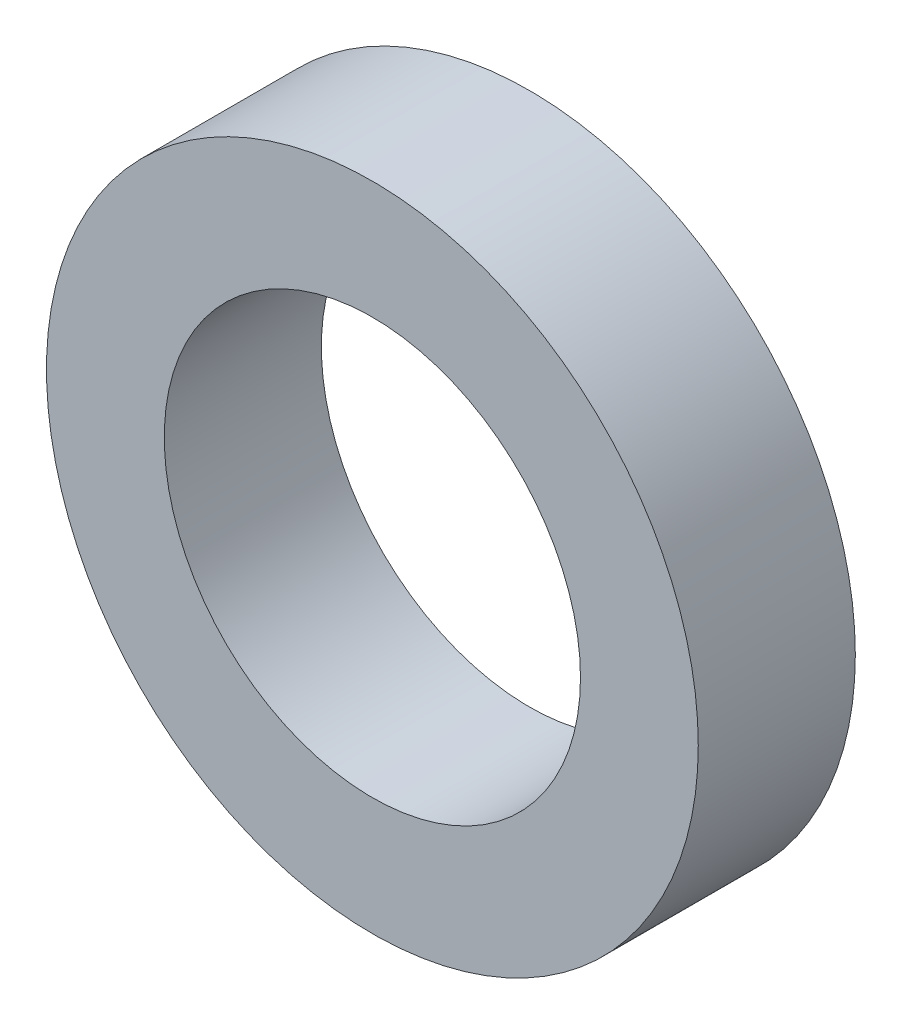
SolidWorks part; units mm, degrees
ref_plane "Front Plane" through (0, 0, 0) normal (0, 0, 1) x (1, 0, 0)
ref_plane "Top Plane" through (0, 0, 0) normal (0, 1, 0) x (1, 0, 0)
ref_plane "Right Plane" through (0, 0, 0) normal (1, 0, 0) x (0, 0, -1)
sketch "Sketch1" plane through (0, 0, 0) normal (0, 0, 1) x (1, 0, 0)
  circle A0 centre (0, 0) radius 2.65
  circle A1 centre (0, 0) radius 4.15
  dimension "D1" = 5.3
  dimension "D2" = 8.3
extrude "Boss-Extrude1" add sketch "Sketch1" along normal blind 2
